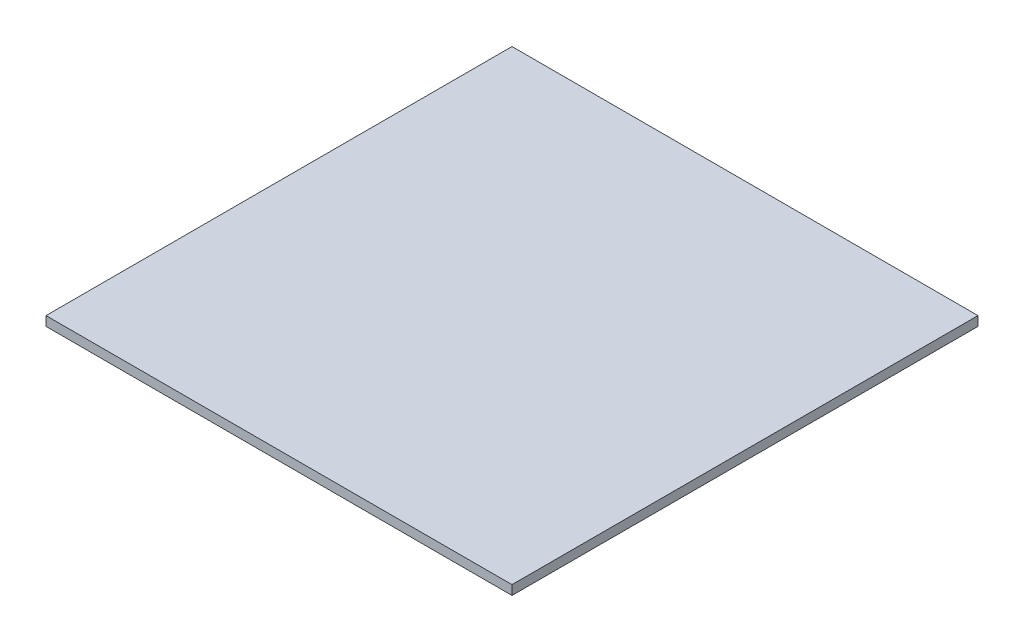
SolidWorks part; units mm, degrees
ref_plane "Front Plane" through (0, 0, 0) normal (0, 0, 1) x (1, 0, 0)
ref_plane "Top Plane" through (0, 0, 0) normal (0, 1, 0) x (1, 0, 0)
ref_plane "Right Plane" through (0, 0, 0) normal (1, 0, 0) x (0, 0, -1)
sketch "Sketch2" plane through (0, 0, 0) normal (0, 1, 0) x (1, 0, 0)
  line L1 (0, 0) -> (150, 0)
  line L2 (0, 0) -> (0, 150)
  line L3 (0, 150) -> (150, 150)
  line L4 (150, 0) -> (150, 150)
  point P5 (135.961, 140.1632)
  point P6 (133.9979, 138.6949)
  point P7 (146.4938, 149.0879)
extrude "Boss-Extrude1" add sketch "Sketch2" along normal blind 3.0212
